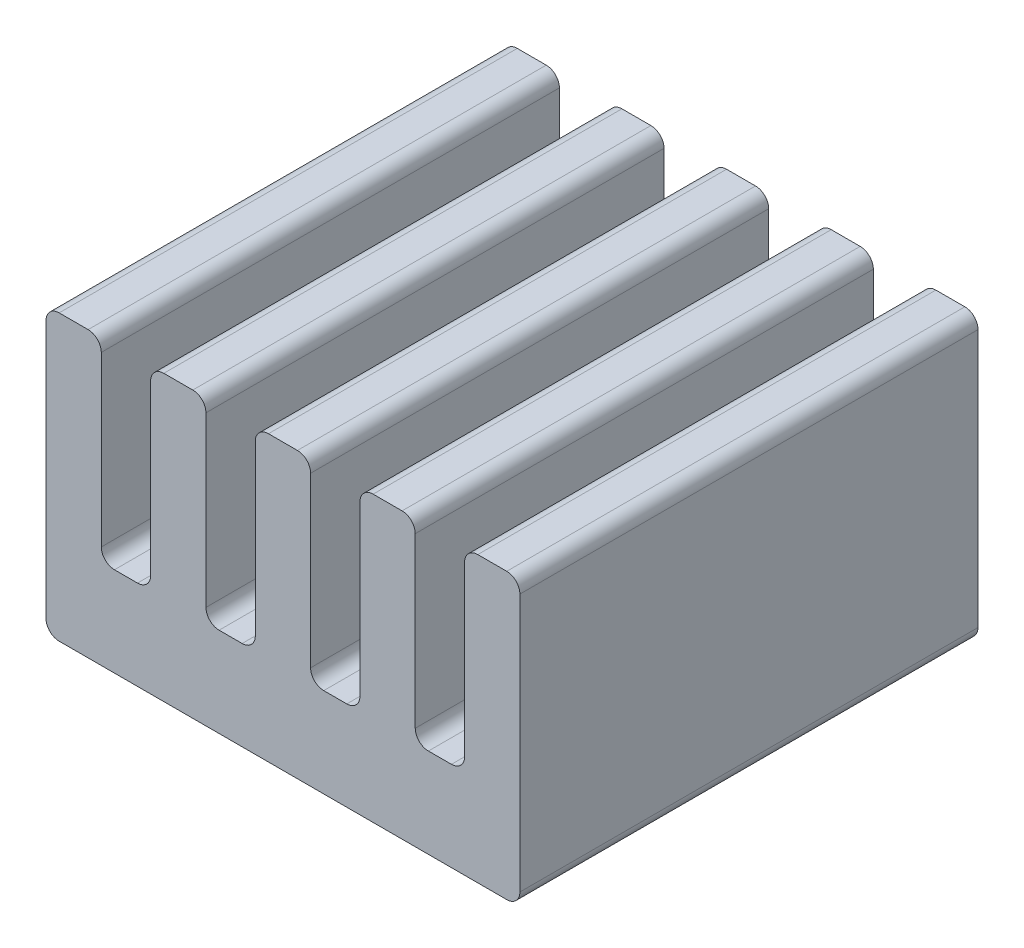
SolidWorks part; units mm, degrees
ref_plane "Front Plane" through (0, 0, 0) normal (0, 0, 1) x (1, 0, 0)
ref_plane "Top Plane" through (0, 0, 0) normal (0, 1, 0) x (1, 0, 0)
ref_plane "Right Plane" through (0, 0, 0) normal (1, 0, 0) x (0, 0, -1)
sketch "Sketch1" plane through (0, 0, 0) normal (0, 0, 1) x (1, 0, 0)
  line L0 (-4.5, 2.7) -> (-4.5, -2.7)
  line L1 (-4.5, -2.7) -> (4.5, -2.7)
  line L2 (0, -2.7) -> (0, 0) construction
  line L3 (-4.5, 2.7) -> (-3.45, 2.7)
  line L4 (-3.45, 2.7) -> (-3.45, -1)
  line L5 (-3.45, -1) -> (-2.5125, -1)
  line L6 (-2.5125, -1) -> (-2.5125, 2.7)
  line L7 (-2.5125, 2.7) -> (-1.4625, 2.7)
  line L8 (-1.4625, 2.7) -> (-1.4625, -1)
  line L9 (-1.4625, -1) -> (-0.525, -1)
  line L10 (-0.525, -1) -> (-0.525, 2.7)
  line L11 (-0.525, 2.7) -> (0.525, 2.7)
  line L12 (0, 2.7) -> (0, 0) construction
  line L13 (0.525, -1) -> (0.525, 2.7)
  line L14 (1.4625, -1) -> (0.525, -1)
  line L15 (1.4625, 2.7) -> (1.4625, -1)
  line L16 (2.5125, 2.7) -> (1.4625, 2.7)
  line L17 (2.5125, -1) -> (2.5125, 2.7)
  line L18 (3.45, -1) -> (2.5125, -1)
  line L19 (3.45, 2.7) -> (3.45, -1)
  line L20 (4.5, 2.7) -> (3.45, 2.7)
  line L21 (4.5, 2.7) -> (4.5, -2.7)
  dimension "D1" = 4.5
  dimension "D2" = 5.4
  dimension "D3" = 2.7
  dimension "D4" = 1.05
  dimension "D5" = 0.525
  dimension "D6" = 1.7
extrude "Boss-Extrude1" add sketch "Sketch1" along normal mid plane 8.7
fillet "Fillet1" radius 0.25 20 edges at (4.5, 2.7, 0) (3.45, 2.7, 0) (3.45, -1, 0) (2.5125, -1, 0) (2.5125, 2.7, 0) (1.4625, 2.7, 0) (1.4625, -1, 0) (0.525, -1, 0) (0.525, 2.7, 0) (-1.4625, -1, 0) (-0.525, -1, 0) (-2.5125, -1, 0) (-3.45, -1, 0) (-0.525, 2.7, 0) (-1.4625, 2.7, 0) (-2.5125, 2.7, 0) (-3.45, 2.7, 0) (-4.5, 2.7, 0) (4.5, -2.7, 0) (-4.5, -2.7, 0)
